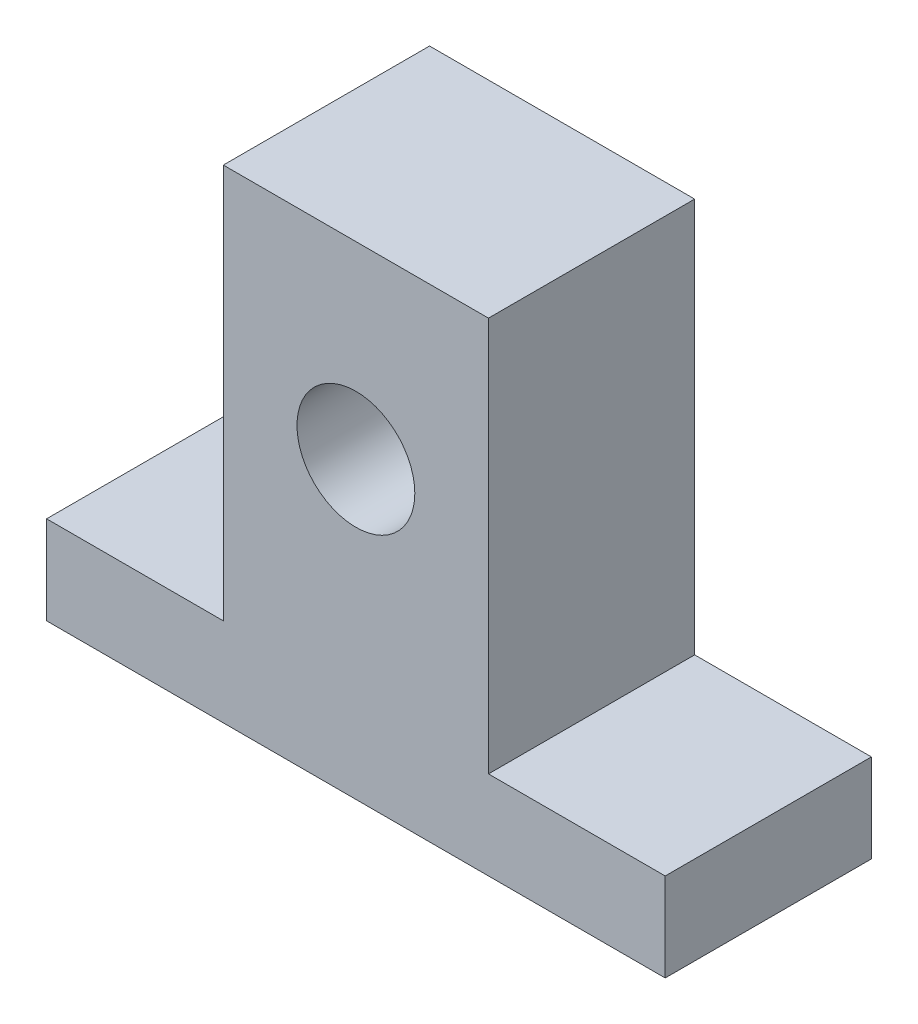
SolidWorks part; units mm, degrees
ref_plane "Front Plane" through (0, 0, 0) normal (0, 0, 1) x (1, 0, 0)
ref_plane "Top Plane" through (0, 0, 0) normal (0, 1, 0) x (1, 0, 0)
ref_plane "Right Plane" through (0, 0, 0) normal (1, 0, 0) x (0, 0, -1)
sketch "Sketch1" plane through (0, 0, 0) normal (0, 0, 1) x (1, 0, 0)
  line L0 (0, 0) -> (42, 0)
  line L1 (42, 0) -> (42, 6)
  line L2 (42, 6) -> (30, 6)
  line L3 (30, 6) -> (30, 32.8)
  line L4 (30, 32.8) -> (12, 32.8)
  line L5 (12, 32.8) -> (12, 6)
  line L6 (12, 6) -> (0, 6)
  line L7 (0, 6) -> (0, 0)
  circle A0 centre (21, 20) radius 4
sketch "Sketch2" plane through (0, 0, 0) normal (0, 0, 1) x (1, 0, 0)
  line L0 (0, 0) -> (42, 0)
  line L1 (42, 0) -> (42, 6)
  line L2 (42, 6) -> (30, 6)
  line L3 (30, 6) -> (30, 32.8)
  line L4 (30, 32.8) -> (12, 32.8)
  line L5 (12, 32.8) -> (12, 6)
  line L6 (12, 6) -> (0, 6)
  line L7 (0, 6) -> (0, 0)
  circle A0 centre (21, 20) radius 4
extrude "Boss-Extrude1" add sketch "Sketch2" along normal blind 14
